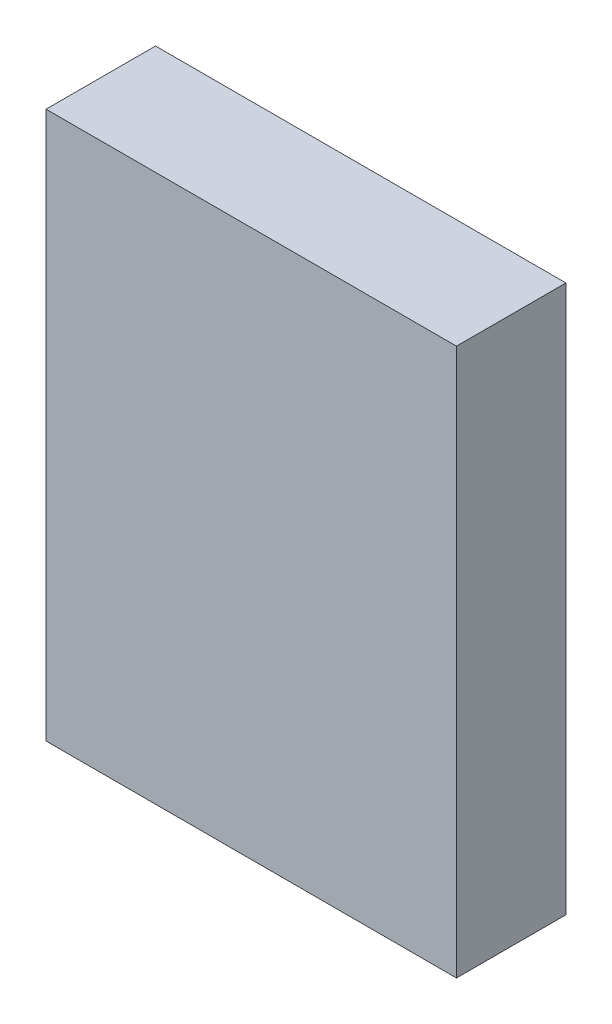
SolidWorks part; units mm, degrees
ref_plane "Plano frontal" through (0, 0, 0) normal (0, 0, 1) x (1, 0, 0)
ref_plane "Plano superior" through (0, 0, 0) normal (0, 1, 0) x (1, 0, 0)
ref_plane "Plano direito" through (0, 0, 0) normal (1, 0, 0) x (0, 0, -1)
sketch "Esboço1" plane through (0, 0, 0) normal (0, 0, 1) x (1, 0, 0)
  line L1 (0, 0) -> (22.5, 0)
  line L2 (0, 0) -> (0, 30)
  line L3 (0, 30) -> (22.5, 30)
  line L4 (22.5, 0) -> (22.5, 30)
  dimension "D1" = 30
  dimension "D2" = 22.5
extrude "Ressalto-extrusão1" add sketch "Esboço1" along normal blind 6
